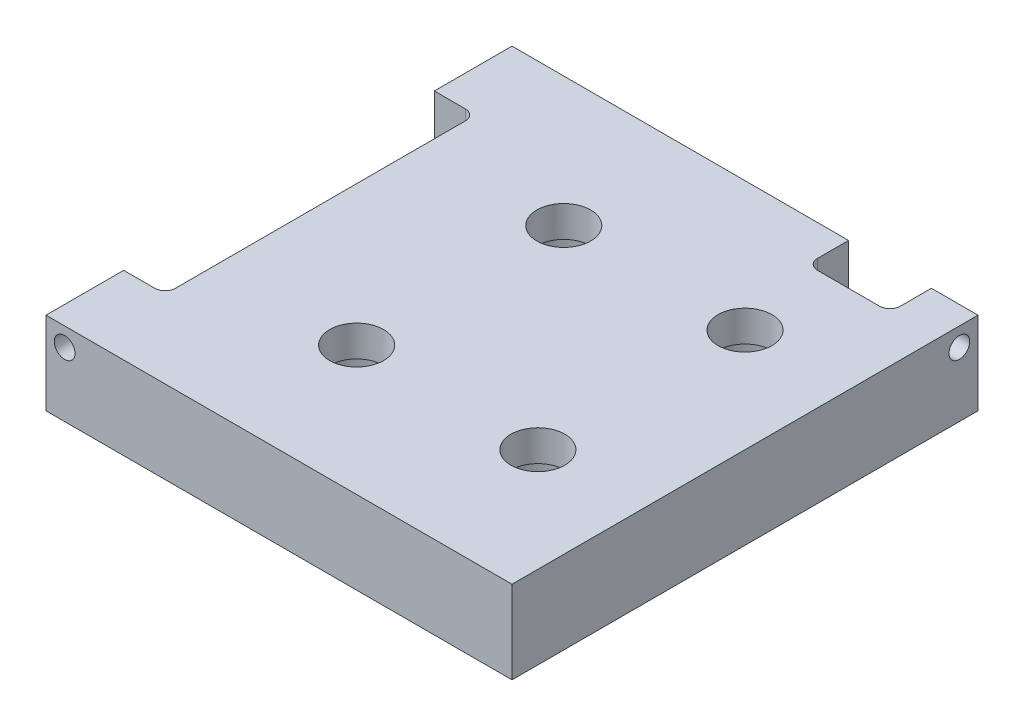
SolidWorks part; units mm, degrees
ref_plane "前视基准面" through (0, 0, 0) normal (0, 0, 1) x (1, 0, 0)
ref_plane "上视基准面" through (0, 0, 0) normal (0, 1, 0) x (1, 0, 0)
ref_plane "右视基准面" through (0, 0, 0) normal (1, 0, 0) x (0, 0, -1)
sketch "草图1" plane through (0, 0, 0) normal (0, 1, 0) x (1, 0, 0)
  line L1 (0, 0) -> (45, 0)
  line L2 (0, 0) -> (0, 45)
  line L3 (0, 45) -> (45, 45)
  line L4 (45, 0) -> (45, 45)
  dimension "D1" = 45
extrude "凸台-拉伸1" add sketch "草图1" along normal blind 8
sketch "草图2" plane through (0, 8, 0) normal (0, 1, 0) x (1, 0, 0)
  line L0 (17.5, 12.5) -> (17.5, 32.5) construction
  line L1 (17.5, 32.5) -> (35, 32.5) construction
  line L2 (35, 32.5) -> (35, 12.5) construction
  line L3 (35, 12.5) -> (17.5, 12.5) construction
  line L4 (45, 22.5) -> (35, 22.5) construction
  line L6 (45, 0) -> (45, 45) construction
  circle A0 centre (17.5, 12.5) radius 2.6
  circle A1 centre (17.5, 32.5) radius 2.6
  circle A2 centre (35, 12.5) radius 2.6
  circle A3 centre (35, 32.5) radius 2.6
  dimension "D1" = 5.2
  dimension "D2" = 20
  dimension "D3" = 17.5
  dimension "D4" = 10
extrude "切除-拉伸1" cut sketch "草图2" against normal through all
sketch "草图3" plane through (0, 0, 0) normal (0, -1, 0) x (-1, 0, 0)
  circle A0 centre (-17.5, 32.5) radius 4.4
  circle A1 centre (-17.5, 12.5) radius 4.4
  circle A2 centre (-35, 12.5) radius 4.4
  circle A3 centre (-35, 32.5) radius 4.4
  dimension "D1" = 8.8
extrude "切除-拉伸2" cut sketch "草图3" against normal blind 5
sketch "草图5" plane through (0, 8, 0) normal (0, 1, 0) x (1, 0, 0)
  line L0 (0, 45) -> (0, 0) construction
  line L1 (0, 37.5) -> (4, 37.5)
  line L2 (0, 37.5) -> (0, 7.5)
  line L3 (0, 7.5) -> (4, 7.5)
  line L4 (4, 37.5) -> (4, 7.5)
  line L5 (2, 37.5) -> (2, 45) construction
  line L6 (45, 45) -> (0, 45) construction
  line L7 (2, 7.5) -> (2, 0) construction
  line L8 (0, 0) -> (45, 0) construction
  dimension "D1" = 30
  dimension "D2" = 4
extrude "切除-拉伸4" cut sketch "草图5" against normal blind 4
sketch "草图6" plane through (0, 0, 0) normal (0, 0, 1) x (1, 0, 0)
  line L0 (0, 4) -> (4, 4) construction
  line L4 (4, 4) -> (4, 8) construction
  circle A0 centre (1.8, 6.2) radius 1
  dimension "D1" = 2
  dimension "D3" = 2.2
  dimension "D2" = 2.2
extrude "切除-拉伸5" cut sketch "草图6" against normal blind 9
fillet "圆角1" radius 1 2 edges at (4, 6, -37.5) (4, 6, -7.5)
sketch "草图7" plane through (0, 8, 0) normal (0, 1, 0) x (1, 0, 0)
  line L0 (40.5, 43) -> (45, 43) construction
  line L1 (45, 45) -> (28, 45) construction
  line L2 (45, 45) -> (45, 41) construction
  line L3 (45, 41) -> (28, 41) construction
  line L4 (28, 45) -> (28, 41) construction
  line L9 (40.5, 41) -> (32.5, 41)
  line L10 (40.5, 41) -> (40.5, 45)
  line L11 (40.5, 45) -> (32.5, 45)
  line L12 (32.5, 41) -> (32.5, 45)
  line L13 (32.5, 43) -> (28, 43) construction
  dimension "D1" = 4
  dimension "D2" = 17
  dimension "D3" = 8
extrude "切除-拉伸6" cut sketch "草图7" against normal blind 4
fillet "圆角2" radius 1 2 edges at (32.5, 6, -41) (40.5, 6, -41)
sketch "草图8" plane through (45, 0, 0) normal (1, 0, 0) x (0, 0, -1)
  line L0 (42, 4) -> (45, 4) construction
  line L1 (41, 8) -> (41, 4) construction
  circle A0 centre (43.2, 6.2) radius 1
  dimension "D1" = 2
  dimension "D3" = 2.2
  dimension "D2" = 2.2
extrude "切除-拉伸7" cut sketch "草图8" against normal blind 9
sketch "草图11" plane through (0, 0, 0) normal (0, -1, 0) x (-1, 0, 0)
  line L0 (-4, 4) -> (-41, 4) construction
  line L1 (-41, 4) -> (-41, 41) construction
  line L2 (-41, 41) -> (-4, 41) construction
  line L3 (-4, 41) -> (-4, 4) construction
  line L4 (-4, 22.5) -> (0, 22.5) construction
  line L5 (0, 45) -> (0, 0) construction
  line L6 (-22.5, 41) -> (-22.5, 45) construction
  line L7 (-45, 45) -> (0, 45) construction
  line L8 (0, 0) -> (-45, 0) construction
  circle A0 centre (-4, 4) radius 1.5
  circle A1 centre (-41, 4) radius 1.5
  circle A2 centre (-4, 41) radius 1.5
  circle A3 centre (-41, 41) radius 1.5
  dimension "D2" = 3
  dimension "D1" = 4
extrude "切除-拉伸10" cut sketch "草图11" against normal blind 3
